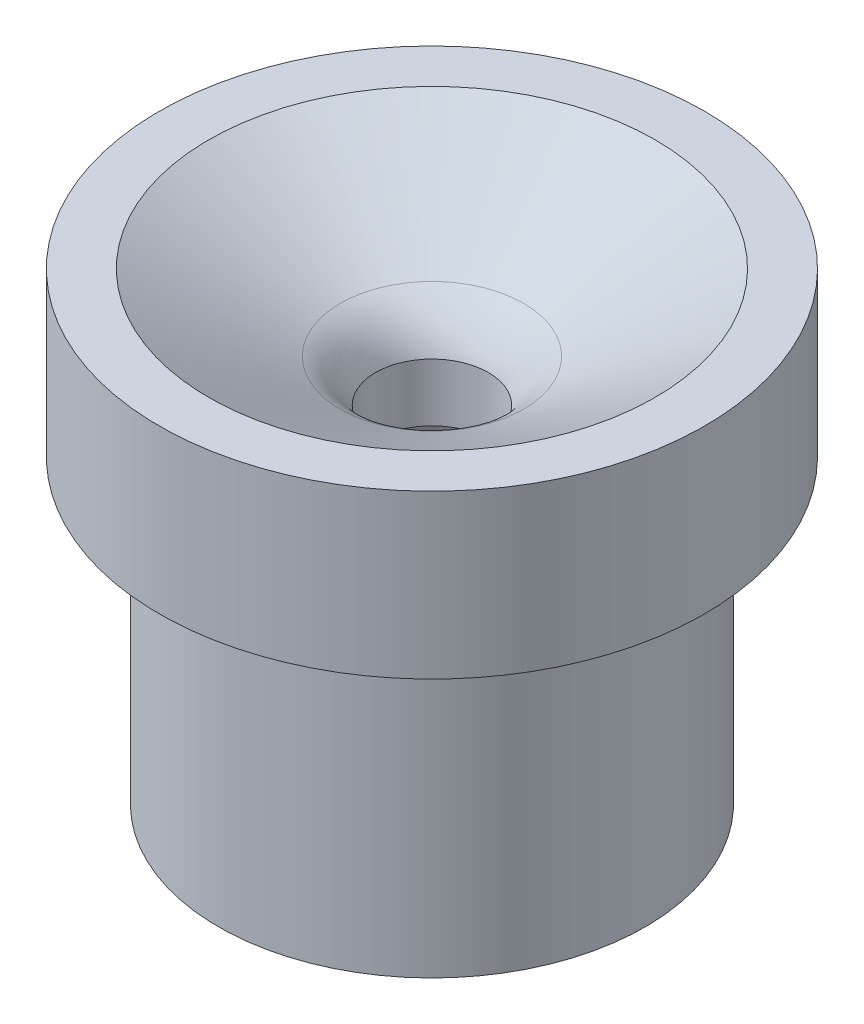
SolidWorks part; units mm, degrees
material "Glass Phenolic"
ref_plane "Front Plane" through (0, 0, 0) normal (0, 0, 1) x (1, 0, 0)
ref_plane "Top Plane" through (0, 0, 0) normal (0, 1, 0) x (1, 0, 0)
ref_plane "Right Plane" through (0, 0, 0) normal (1, 0, 0) x (0, 0, -1)
sketch "Sketch1" plane through (0, 0, 0) normal (0, 0, 1) x (1, 0, 0)
  line L0 (0, 0) -> (0, 5.7042) construction
  line L1 (-6.1595, 0) -> (-6.1595, 1.5875)
  line L2 (-6.1595, 0) -> (-15.8954, -36.3347)
  line L3 (-15.8954, -36.3347) -> (-25.4, -36.3347)
  line L4 (-25.4, -36.3347) -> (-25.4, -0.503)
  line L5 (-25.4, -0.503) -> (-32.4739, -0.503)
  line L6 (-32.4739, -0.503) -> (-32.4739, 18.8772)
  line L7 (-32.4739, 18.8772) -> (-26.5811, 18.8772)
  line L8 (-26.5811, 18.8772) -> (-10.922, 9.8364)
  line L9 (-6.1595, 0) -> (0, 0) construction
  arc A0 (-10.922, 9.8364) -> (-6.1595, 1.5875) centre (-15.6845, 1.5875) cw
  point P13 (-6.1595, 0.7937)
  dimension "D3" = 9.525
  dimension "D1" = 1.5875
  dimension "D2" = 6.1595
  dimension "D4" = 26.5811
  dimension "D5" = 60
  dimension "D6" = 36.3347
  dimension "D7" = 15
  dimension "D8" = 25.4
  dimension "D9" = 32.4739
  dimension "D10" = 19.3802
revolve "Revolve1" add sketch "Sketch1" angle 360 about L0
sketch "Sketch2" plane through (0, 18.8772, 0) normal (0, 1, 0) x (1, 0, 0)
  circle A0 centre (0, 0) radius 6.7183
  dimension "D1" = 13.4366
extrude "Cut-Extrude1" cut sketch "Sketch2" against normal through all
